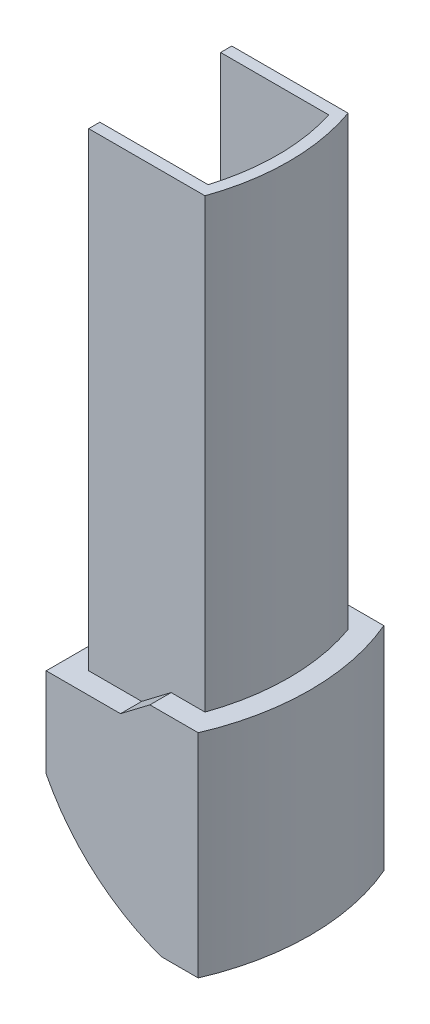
SolidWorks part; units mm, degrees
ref_plane "Front Plane" through (0, 0, 0) normal (0, 0, 1) x (1, 0, 0)
ref_plane "Top Plane" through (0, 0, 0) normal (0, 1, 0) x (1, 0, 0)
ref_plane "Right Plane" through (0, 0, 0) normal (1, 0, 0) x (0, 0, -1)
sketch "Sketch1" plane through (0, 0, 0) normal (0, 0, 1) x (1, 0, 0)
  line L0 (0, 0) -> (-5, 0)
  line L1 (0, 0) -> (0, 19)
  line L2 (0, 19) -> (-6.0223, 19)
  line L3 (-6.0223, 19) -> (-8.6559, 17)
  line L4 (-8.6559, 17) -> (-15.3, 17)
  line L5 (-15.3, 17) -> (-15.3, 9)
  line L6 (-11.0103, 3.5154) -> (0, 19) construction
  arc A0 (-5, 0) -> (-15.3, 9) centre (1.1886, 17.4764) cw
  dimension "D1" = 15.3
  dimension "D2" = 19
  dimension "D3" = 5
  dimension "D4" = 2
  dimension "D5" = 8
  dimension "D6" = 19
extrude "Boss-Extrude1" add sketch "Sketch1" along normal blind 16.6
sketch "Sketch2" plane through (0, 0, 0) normal (0, -1, 0) x (1, 0, 0)
  line L0 (-5, 16.6) -> (0, 16.6) construction
  line L1 (-5, 0) -> (0, 0) construction
  line L3 (0, 16.6) -> (0, 0) construction
  line L4 (-1.7, 0) -> (-1.7, 16.6) construction
  line L5 (-15.3, 16.6) -> (-15.3, 0) construction
  line L6 (-1.7, 16.6) -> (0, 16.6)
  line L7 (0, 16.6) -> (0, 0)
  line L8 (0, 0) -> (-1.7, 0)
  arc A0 (-1.7, 16.6) -> (-1.7, 0) centre (-21.1118, 8.3) cw
  line M3 (-5, 0) -> (0, 0)
  line M4 (0, 0) -> (0, 16.6)
  line M5 (0, 16.6) -> (-5, 16.6)
  dimension "D1" = 13.6
extrude "Cut-Extrude1" cut sketch "Sketch2" against normal through all contours A0 L7 M5 | A0 M4 M3
ref_plane "Plane1" through (0, 29, 0) normal (0, 1, 0) x (1, 0, 0)
sketch "Sketch3" plane through (0, 29, 0) normal (0, 1, 0) x (1, 0, 0)
  line L0 (-15.3, 0) -> (-1.7, 0) construction
  line L1 (-15.3, -16.6) -> (-1.7, -16.6) construction
  line L2 (-15.3, 0) -> (-15.3, -16.6) construction
  line L3 (-13.4, -1.9) -> (-2.9974, -1.9)
  line L4 (-13.4, -14.7) -> (-2.9974, -14.7)
  line L5 (-13.4, -1.9) -> (-13.4, -2.9)
  line L6 (-12.4, -2.9) -> (-3.719, -2.9)
  line L7 (-12.4, -13.7) -> (-3.719, -13.7)
  line L9 (-12.4, -2.9) -> (-13.4, -2.9)
  line L10 (-12.4, -13.7) -> (-13.4, -13.7)
  line L11 (-13.4, -13.7) -> (-13.4, -14.7)
  line L13 (-13.4, -1.9) -> (-13.4, -14.7) construction
  line L14 (-12.4, -2.9) -> (-12.4, -13.7) construction
  arc A0 (-1.7, 0) -> (-1.7, -16.6) centre (-21.1118, -8.3) cw construction
  arc A1 (-1.7, -16.6) -> (-1.7, 0) centre (-21.1118, -8.3) ccw construction
  arc A2 (-2.9974, -1.9) -> (-2.9974, -14.7) centre (-21.1118, -8.3) cw
  arc A3 (-3.719, -2.9) -> (-3.719, -13.7) centre (-21.1118, -8.3) cw
  dimension "D1" = 1.9
  dimension "D2" = 1
extrude "Boss-Extrude2" add sketch "Sketch3" against normal up to body (30 mm away) and the other way blind 16.6 separate body
